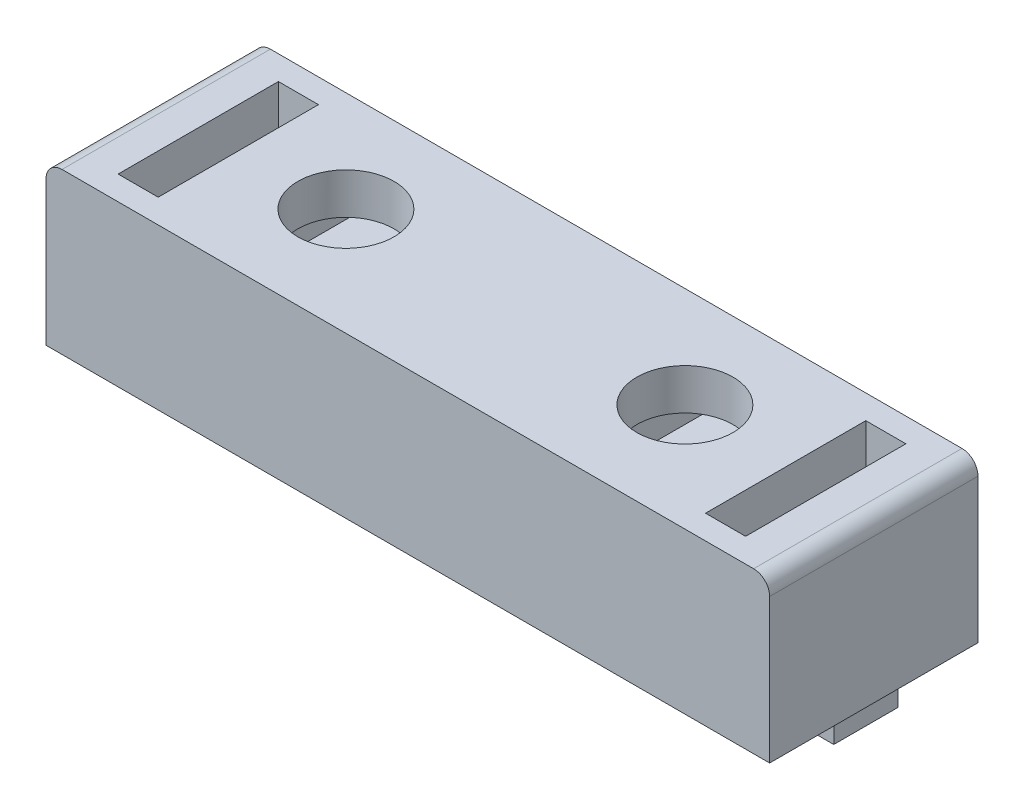
SolidWorks part; units mm, degrees
material "ABS"
ref_plane "Front Plane" through (0, 0, 0) normal (0, 0, 1) x (1, 0, 0)
ref_plane "Top Plane" through (0, 0, 0) normal (0, 1, 0) x (1, 0, 0)
ref_plane "Right Plane" through (0, 0, 0) normal (1, 0, 0) x (0, 0, -1)
sketch "Sketch1" plane through (0, 0, 0) normal (0, 1, 0) x (1, 0, 0)
  line L1 (-27.9927, 12.573) -> (62.3073, 12.573)
  line L2 (-27.9927, 12.573) -> (-27.9927, -13.427)
  line L3 (-27.9927, -13.427) -> (62.3073, -13.427)
  line L4 (62.3073, 12.573) -> (62.3073, -13.427)
  dimension "D1" = 26
  dimension "D2" = 90.3
extrude "Boss-Extrude1" add sketch "Sketch1" against normal blind 20
sketch "Sketch2" plane through (0, 0, 0) normal (0, 1, 0) x (1, 0, 0)
  line L5 (62.3073, 12.573) -> (-27.9927, 12.573) construction
  line L6 (62.3073, -13.427) -> (62.3073, 12.573) construction
  line L7 (51.3073, -10.427) -> (56.3073, -10.427)
  line L8 (51.3073, -10.427) -> (51.3073, 9.573)
  line L9 (51.3073, 9.573) -> (56.3073, 9.573)
  line L10 (56.3073, -10.427) -> (56.3073, 9.573)
  dimension "D5" = 6
  dimension "D6" = 20
  dimension "D8" = 5
extrude "Cut-Extrude1" cut sketch "Sketch2" against normal through all
pattern_linear "LPattern1" count 2 spacing 73.3 along (-1, 0, 0) of "Cut-Extrude1"
sketch "Sketch3" plane through (0, 0, 0) normal (0, 1, 0) x (1, 0, 0)
  line L3 (-16.9927, -10.427) -> (-16.9927, 9.573) construction
  line L4 (51.3073, 9.573) -> (51.3073, -10.427) construction
  circle A0 centre (38.3073, 0) radius 6
  circle A1 centre (-3.9927, 0) radius 6
  dimension "D1" = 12
  dimension "D3" = 12
  dimension "D2" = 13
  dimension "D4" = 13
extrude "Cut-Extrude2" cut sketch "Sketch3" against normal blind 18
sketch "Sketch4" plane through (0, 0, -12.573) normal (0, 0, -1) x (-1, 0, 0)
  line L1 (-48.3073, -5.1291) -> (-29.3073, -5.1291)
  line L2 (-48.3073, -5.1291) -> (-48.3073, -11.1291)
  line L3 (-48.3073, -11.1291) -> (-29.3073, -11.1291)
  line L4 (-29.3073, -5.1291) -> (-29.3073, -11.1291)
  line L6 (-5.0073, -5.1291) -> (13.9927, -5.1291)
  line L7 (-5.0073, -5.1291) -> (-5.0073, -11.1291)
  line L8 (-5.0073, -11.1291) -> (13.9927, -11.1291)
  line L9 (13.9927, -5.1291) -> (13.9927, -11.1291)
  line L10 (-62.3073, -20) -> (-62.3073, 0) construction
  line L11 (27.9927, -20) -> (27.9927, 0) construction
  dimension "D1" = 14
  dimension "D2" = 19
  dimension "D3" = 6
  dimension "D4" = 14
  dimension "D5" = 6
  dimension "D6" = 19
extrude "Cut-Extrude3" cut sketch "Sketch4" against normal blind 22.5
sketch "Sketch5" plane through (0, -20, 0) normal (0, -1, 0) x (1, 0, 0)
  line L0 (62.3073, 13.427) -> (62.3073, -12.573) construction
  line L1 (61.3073, -3.573) -> (58.3073, -3.573)
  line L2 (61.3073, -3.573) -> (61.3073, 4.427)
  line L3 (61.3073, 4.427) -> (58.3073, 4.427)
  line L4 (58.3073, -3.573) -> (58.3073, 4.427)
  line L5 (62.3073, -12.573) -> (-27.9927, -12.573) construction
  line L7 (-26.4927, 4.427) -> (-23.4927, 4.427)
  line L8 (-26.4927, 4.427) -> (-26.4927, -3.573)
  line L9 (-26.4927, -3.573) -> (-23.4927, -3.573)
  line L10 (-23.4927, 4.427) -> (-23.4927, -3.573)
  line L11 (-27.9927, 13.427) -> (62.3073, 13.427) construction
  line L12 (-27.9927, -12.573) -> (-27.9927, 13.427) construction
  point P4 (59.8073, 4.427)
  point P7 (59.8073, -3.573)
  dimension "D1" = 3
  dimension "D2" = 2.5
  dimension "D3" = 8
  dimension "D4" = 9
  dimension "D5" = 8
  dimension "D6" = 3
  dimension "D7" = 1.5
  dimension "D8" = 9
extrude "Boss-Extrude2" add sketch "Sketch5" along normal blind 3
fillet "Fillet1" radius 2 2 edges at (62.3073, 0, 0.427) (-27.9927, 0, 0.427)
